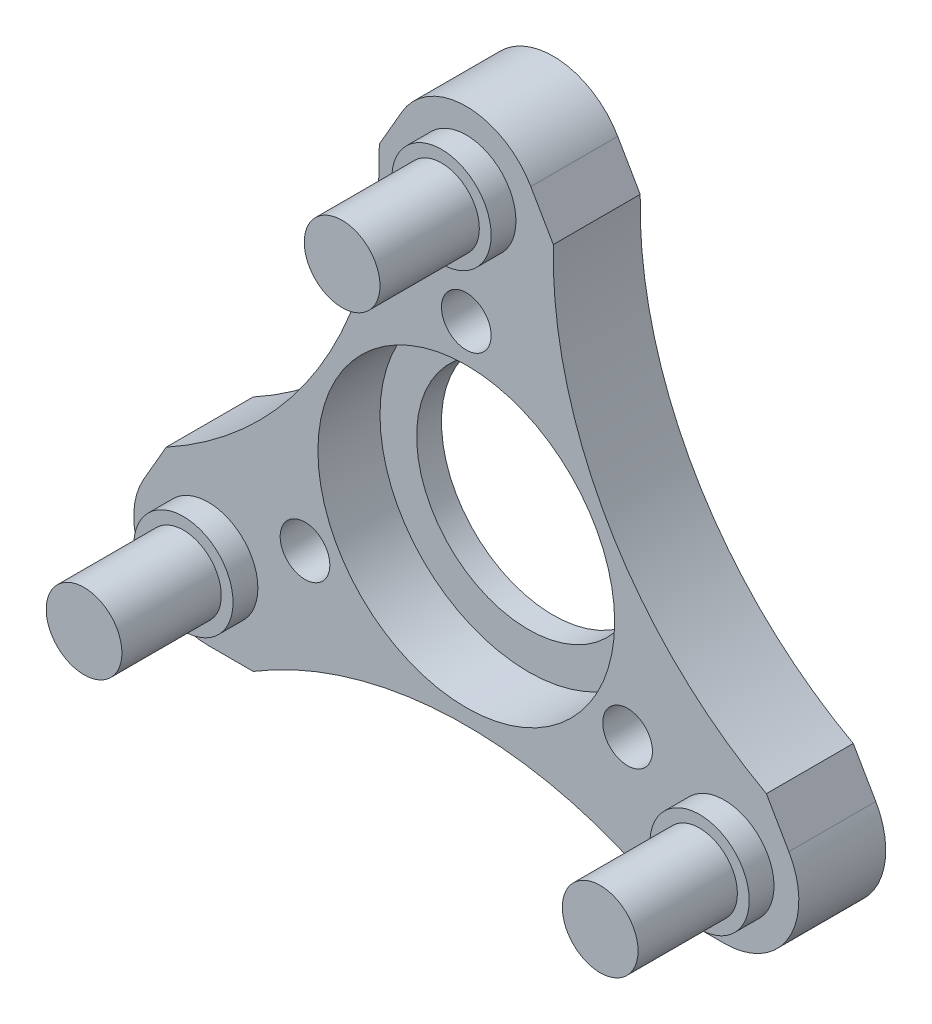
SolidWorks part; units mm, degrees
ref_plane "前视基准面" through (0, 0, 0) normal (0, 0, 1) x (1, 0, 0)
ref_plane "上视基准面" through (0, 0, 0) normal (0, 1, 0) x (1, 0, 0)
ref_plane "右视基准面" through (0, 0, 0) normal (1, 0, 0) x (0, 0, -1)
sketch "草图1" plane through (0, 0, 0) normal (0, 0, 1) x (1, 0, 0)
  line L0 (-34.0424, 0) -> (27.8753, 0) construction
  line L1 (0, 25.6551) -> (0, -31.8222) construction
  line L2 (0, 12) -> (-10.3923, -6)
  line L3 (-10.3923, -6) -> (10.3923, -6)
  line L4 (10.3923, -6) -> (0, 12)
  line L5 (0, 18) -> (-15.5885, -9)
  line L6 (-15.5885, -9) -> (15.5885, -9)
  line L7 (15.5885, -9) -> (0, 18)
  dimension "D1" = 60
  dimension "D2" = 60
  dimension "D3" = 12
  dimension "D4" = 12
  dimension "D5" = 3
extrude "凸台-拉伸1" add sketch "草图1" along normal blind 2.5 contours L3 L4 L2 | L6 L7 L5 L4 L3 L2
fillet "圆角1" radius 3 3 edges at (-15.5885, -9, 1.25) (15.5885, -9, 1.25) (0, 18, 1.25)
sketch "草图2" plane through (0, 0, 2.5) normal (0, 0, 1) x (1, 0, 0)
  line L0 (0, 12) -> (-10.3923, -6) construction
  line L1 (-10.3923, -6) -> (10.3923, -6) construction
  line L2 (10.3923, -6) -> (0, 12) construction
  line L3 (0, 12) -> (0, 0) construction
  line L4 (0, 0) -> (-5.1962, 3) construction
  circle A0 centre (0, 12) radius 1.525
  circle A1 centre (10.3923, -6) radius 1.525
  circle A2 centre (-10.3923, -6) radius 1.525
  point P6 (0, 0)
  dimension "D1" = 3.05
  dimension "D2" = 12
  dimension "D3" = 60
  dimension "D4" = 60
extrude "凸台-拉伸2" add sketch "草图2" along normal blind 5
sketch "草图3" plane through (0, 0, 2.5) normal (0, 0, 1) x (1, 0, 0)
  line L0 (0, 12) -> (-10.3923, -6) construction
  line L1 (-10.3923, -6) -> (10.3923, -6) construction
  line L2 (10.3923, -6) -> (0, 12) construction
  line L3 (0, 12) -> (0, 0) construction
  line L4 (0, 0) -> (-5.1962, 3) construction
  circle A0 centre (0, 12) radius 2
  circle A1 centre (10.3923, -6) radius 2
  circle A2 centre (-10.3923, -6) radius 2
  point P6 (0, 0)
  dimension "D1" = 4
  dimension "D2" = 12
  dimension "D3" = 60
  dimension "D4" = 60
extrude "凸台-拉伸3" add sketch "草图3" along normal blind 1
sketch "草图4" plane through (0, 0, 0) normal (0, 0, -1) x (-1, 0, 0)
  circle A0 centre (0, 0) radius 5.975
  dimension "D1" = 11.95
extrude "切除-拉伸1" cut sketch "草图4" against normal blind 10
sketch "草图5" plane through (0, 0, 0) normal (0, 0, -1) x (-1, 0, 0)
  line L3 (-10.3923, -9) -> (10.3923, -9)
  line L4 (12.9904, -4.5) -> (2.5981, 13.5)
  line L5 (-2.5981, 13.5) -> (-12.9904, -4.5)
  line L6 (-10.3923, -9) -> (10.3923, -9)
  line L7 (12.9904, -4.5) -> (2.5981, 13.5)
  line L8 (-2.5981, 13.5) -> (-12.9904, -4.5)
  arc A3 (10.3923, -9) -> (12.9904, -4.5) centre (10.3923, -6) ccw
  arc A4 (2.5981, 13.5) -> (-2.5981, 13.5) centre (0, 12) ccw
  arc A5 (-12.9904, -4.5) -> (-10.3923, -9) centre (-10.3923, -6) ccw
  arc A6 (10.3923, -9) -> (12.9904, -4.5) centre (10.3923, -6) ccw
  arc A7 (2.5981, 13.5) -> (-2.5981, 13.5) centre (0, 12) ccw
  arc A8 (-12.9904, -4.5) -> (-10.3923, -9) centre (-10.3923, -6) ccw
  dimension "D1" = 0
extrude "凸台-拉伸4" add sketch "草图5" along normal blind 1
sketch "草图6" plane through (0, 0, 0) normal (0, 0, 1) x (1, 0, 0)
  circle A0 centre (0, 0) radius 4.5
  dimension "D1" = 9
extrude "切除-拉伸2" cut sketch "草图6" against normal blind 1
sketch "草图7" plane through (0, 0, 2.5) normal (0, 0, 1) x (1, 0, 0)
  circle A0 centre (0, 0) radius 7.5 construction
  circle A1 centre (0, 7.5) radius 1
  circle A2 centre (6.4952, -3.75) radius 1
  circle A3 centre (-6.4952, -3.75) radius 1
  point P11 (0, 0)
  dimension "D1" = 15
  dimension "D2" = 2
  dimension "D3" = 3
extrude "切除-拉伸3" cut sketch "草图7" against normal blind 10
sketch "草图8" plane through (0, 0, -1) normal (0, 0, -1) x (-1, 0, 0)
  arc A3 (7.3612, -3.25) -> (6.4952, -4.75) centre (6.4952, -3.75) cw
  dimension "D1" = 1
sketch "草图9" plane through (0, 0, 2.5) normal (0, 0, 1) x (1, 0, 0)
  line L0 (-20, 11.547) -> (20, 11.547) construction
  line L1 (20, 11.547) -> (0, -23.094) construction
  line L2 (0, -23.094) -> (-20, 11.547) construction
  line L3 (0, 11.547) -> (0, 0) construction
  line L4 (20, 11.547) -> (0, 0) construction
  circle A0 centre (-20, 11.547) radius 16.5
  circle A1 centre (20, 11.547) radius 16.5
  circle A2 centre (0, -23.094) radius 16.5
  point P8 (0, 0)
  dimension "D4" = 33
  dimension "D1" = 60
  dimension "D2" = 60
  dimension "D3" = 40
  dimension "D5" = 60
extrude "切除-拉伸4" cut sketch "草图9" against normal blind 10
